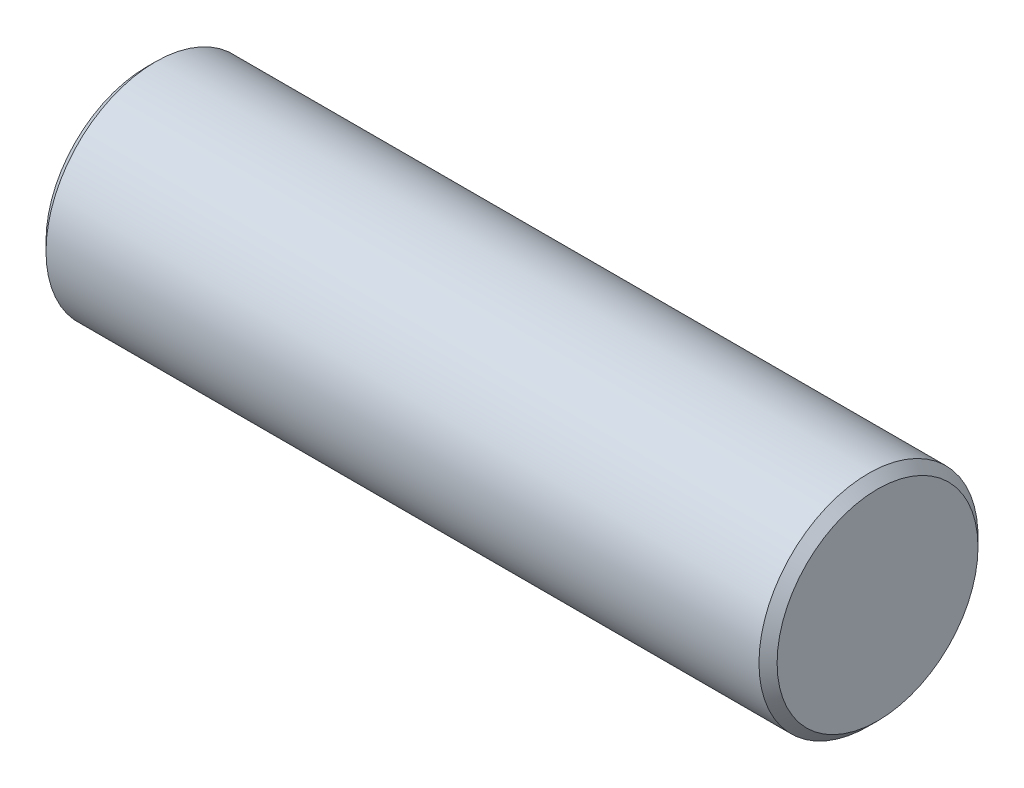
SolidWorks part; units mm, degrees
ref_plane "Front Plane" through (0, 0, 0) normal (0, 0, 1) x (1, 0, 0)
ref_plane "Top Plane" through (0, 0, 0) normal (0, 1, 0) x (1, 0, 0)
ref_plane "Right Plane" through (0, 0, 0) normal (1, 0, 0) x (0, 0, -1)
sketch "Sketch2" plane through (0, 0, 0) normal (0, 0, 1) x (1, 0, 0)
  line L0 (-2.3127, 0) -> (3.5969, 0) construction
  line L1 (-2.5, 0.749) -> (2.5, 0.749)
  line L5 (-2.5, 0.749) -> (-2.5, 0)
  line L6 (2.5, 0.749) -> (2.5, 0)
  line L7 (-2.5, 0) -> (2.5, 0)
  point P6 (-2.3127, 0)
  point P7 (2.9873, 0)
  dimension "D1" = 0.749
  dimension "D2" = 5
  dimension "D3" = 2.5
revolve "Revolve1" add sketch "Sketch2" angle 360 about L0
chamfer "Chamfer1" distance 0.062 angle 45 2 edges at (2.5, 0, 0.749) (-2.5, 0, 0.749)
